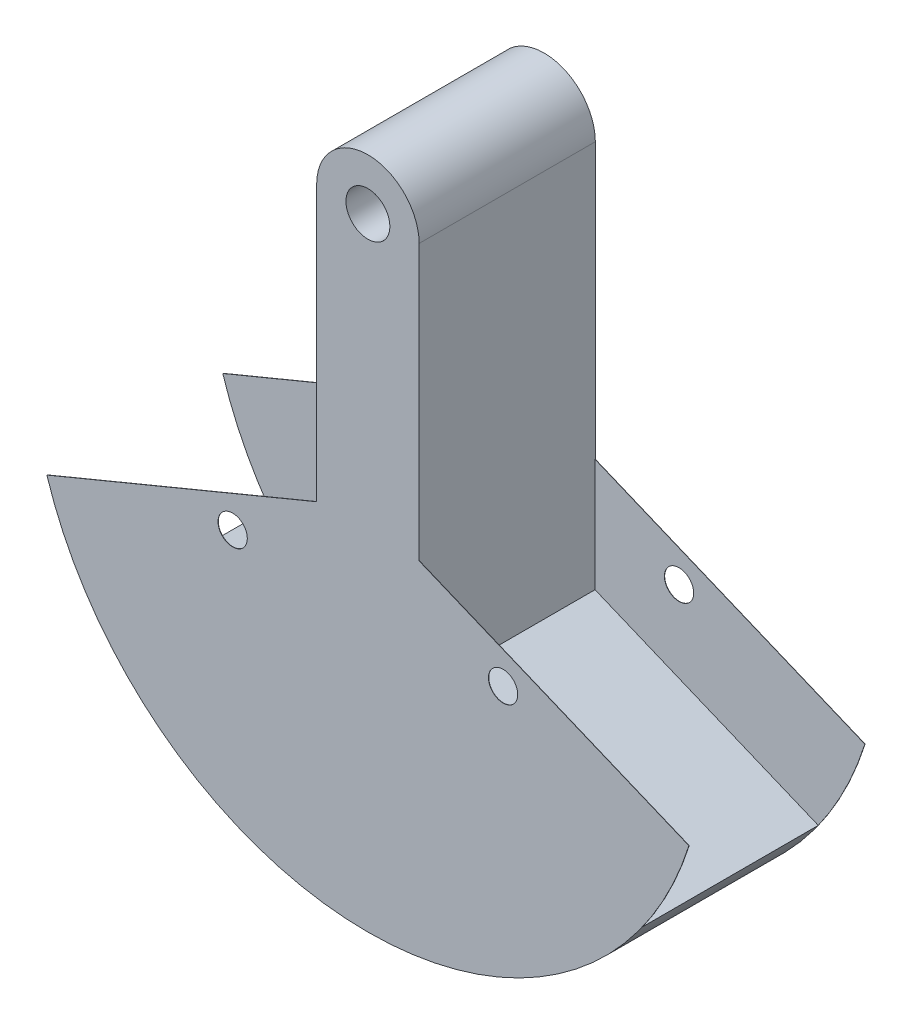
SolidWorks part; units mm, degrees
material "AISI 1020"
ref_plane "Front Plane" through (0, 0, 0) normal (0, 0, 1) x (1, 0, 0)
ref_plane "Top Plane" through (0, 0, 0) normal (0, 1, 0) x (1, 0, 0)
ref_plane "Right Plane" through (0, 0, 0) normal (1, 0, 0) x (0, 0, -1)
other "Center of Mass"
sketch "Sketch1" plane through (0, 0, 0) normal (0, 0, 1) x (1, 0, 0)
  line L0 (0, 0) -> (-117.3327, -48.6008) construction
  line L1 (0, 292.1) -> (0, -292.1) construction
  line L2 (117.3327, -48.6008) -> (0, 0) construction
  line L3 (0, 247.65) -> (0, 0) construction
  line L4 (44.45, 247.65) -> (44.45, -88.9)
  line L5 (-44.45, 247.65) -> (-44.45, -88.9)
  line L6 (-44.45, -88.9) -> (-238.1516, -169.1338)
  line L7 (44.45, -88.9) -> (238.1516, -169.1338)
  circle A0 centre (0, 0) radius 292.1 construction
  circle A1 centre (0, 0) radius 127 construction
  circle A2 centre (-117.3327, -48.6008) radius 12.7 construction
  circle A3 centre (117.3327, -48.6008) radius 12.7 construction
  circle A4 centre (0, 247.65) radius 19.05
  arc A5 (44.45, 247.65) -> (-44.45, 247.65) centre (0, 247.65) ccw
  arc A7 (-238.1516, -169.1338) -> (238.1516, -169.1338) centre (0, 0) ccw
  dimension "D1" = 584.2
  dimension "D2" = 254
  dimension "D5" = 25.4
  dimension "D8" = 135
  dimension "D9" = 381
  dimension "D6" = 38.1
  dimension "D7" = 25.4
  dimension "D3" = 135
  dimension "D4" = 67.5
extrude "Boss-Extrude2" add sketch "Sketch1" along normal mid plane 152.4 contours L6 A7 L7 L4 A5 L5 A4
sketch "Sketch3" plane through (0, 0, 76.2) normal (0, 0, 1) x (1, 0, 0)
  line L0 (0, 0) -> (-117.3327, -48.6008) construction
  line L1 (0, 292.1) -> (0, -292.1) construction
  line L2 (117.3327, -48.6008) -> (0, 0) construction
  line L3 (0, 247.65) -> (0, 0) construction
  line L4 (44.45, 247.65) -> (44.45, 9.081)
  line L5 (-44.45, 247.65) -> (-44.45, 9.081)
  line L6 (-44.45, 9.081) -> (-278.5632, -87.8919)
  line L7 (44.45, 9.081) -> (278.5632, -87.8919)
  circle A0 centre (0, 0) radius 292.1 construction
  circle A1 centre (0, 0) radius 127 construction
  circle A2 centre (-117.3327, -48.6008) radius 12.7
  circle A3 centre (117.3327, -48.6008) radius 12.7
  circle A4 centre (0, 247.65) radius 19.05
  arc A5 (44.45, 247.65) -> (-44.45, 247.65) centre (0, 247.65) ccw
  arc A6 (-278.5632, -87.8919) -> (278.5632, -87.8919) centre (0, 0) ccw
  circle A7 centre (0, 247.65) radius 19.05 construction
  dimension "D1" = 584.2
  dimension "D2" = 254
  dimension "D5" = 25.4
  dimension "D6" = 38.1
  dimension "D3" = 135
  dimension "D4" = 67.5
  dimension "D7" = 25.4
extrude "Boss-Extrude4" add sketch "Sketch3" along normal blind 0.254 contours L6 A6 L7 L4 A5 L5
mirror "Mirror4" about plane through (0, 0, 0) normal (0, 0, 1) of "Boss-Extrude4"
